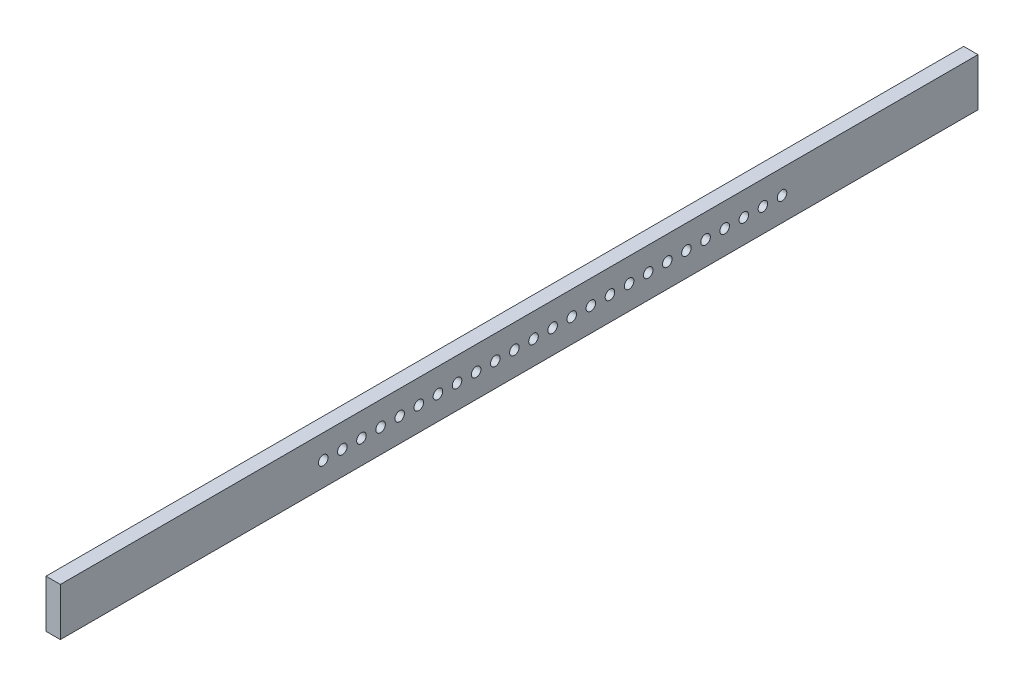
SolidWorks part; units mm, degrees
ref_plane "Front Plane" through (0, 0, 0) normal (0, 0, 1) x (1, 0, 0)
ref_plane "Top Plane" through (0, 0, 0) normal (0, 1, 0) x (1, 0, 0)
ref_plane "Right Plane" through (0, 0, 0) normal (1, 0, 0) x (0, 0, -1)
sketch "Sketch1" plane through (0, 0, 0) normal (1, 0, 0) x (0, 0, -1)
  line L0 (-677.4303, 0) -> (702.5039, 0) construction
  line L1 (-480, 25) -> (480, 25)
  line L2 (-480, 25) -> (-480, -25)
  line L3 (-480, -25) -> (480, -25)
  line L4 (480, 25) -> (480, -25)
  line L5 (-480, 25) -> (480, -25) construction
  line L6 (-480, -25) -> (480, 25) construction
  circle A0 centre (-205, 0) radius 5
  circle A1 centre (-185, 0) radius 5
  circle A2 centre (-165, 0) radius 5
  circle A3 centre (-145, 0) radius 5
  circle A4 centre (-125, 0) radius 5
  circle A5 centre (-105, 0) radius 5
  circle A6 centre (-85, 0) radius 5
  circle A7 centre (-65, 0) radius 5
  circle A8 centre (-45, 0) radius 5
  circle A9 centre (-25, 0) radius 5
  circle A10 centre (-5, 0) radius 5
  circle A11 centre (15, 0) radius 5
  circle A12 centre (35, 0) radius 5
  circle A13 centre (55, 0) radius 5
  circle A14 centre (75, 0) radius 5
  circle A15 centre (95, 0) radius 5
  circle A16 centre (115, 0) radius 5
  circle A17 centre (135, 0) radius 5
  circle A18 centre (155, 0) radius 5
  circle A19 centre (175, 0) radius 5
  circle A20 centre (195, 0) radius 5
  circle A21 centre (215, 0) radius 5
  circle A22 centre (235, 0) radius 5
  circle A23 centre (255, 0) radius 5
  circle A24 centre (275, 0) radius 5
  point P0 (0, 0)
  dimension "D3" = 10
  dimension "D1" = 960
  dimension "D2" = 50
  dimension "D4" = 275
  dimension "D6" = 20
  dimension "D5" = 25
extrude "Boss-Extrude1" add sketch "Sketch1" along normal blind 15
